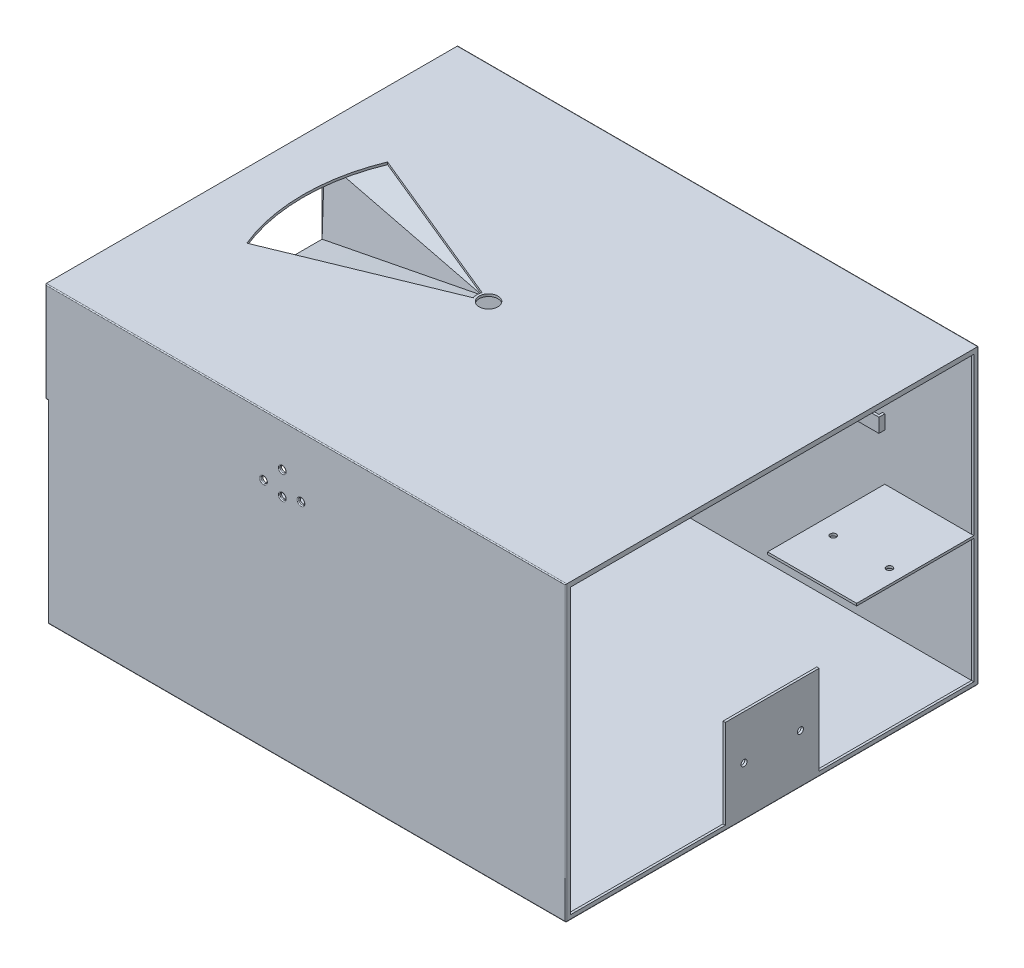
SolidWorks part; units mm, degrees
ref_plane "Front Plane" through (0, 0, 0) normal (0, 0, 1) x (1, 0, 0)
ref_plane "Top Plane" through (0, 0, 0) normal (0, 1, 0) x (1, 0, 0)
ref_plane "Right Plane" through (0, 0, 0) normal (1, 0, 0) x (0, 0, -1)
sketch "Sketch3" plane through (0, 0, 0) normal (1, 0, 0) x (0, 0, -1)
  line L0 (-124, -34.7838) -> (50, -34.7838)
  line L1 (-125, -158.7838) -> (51, -158.7838)
  line L2 (-125, -158.7838) -> (-125, -33.7838)
  line L3 (-125, -33.7838) -> (51, -33.7838)
  line L4 (51, -158.7838) -> (51, -33.7838)
  line L7 (-124, -157.7838) -> (-124, -34.7838)
  line L8 (-124, -157.7838) -> (50, -157.7838)
  line L9 (50, -157.7838) -> (50, -34.7838)
  line L11 (50, -158.7838) -> (50, -33.7838) construction
  line L13 (-125, -34.7838) -> (51, -34.7838) construction
  line L14 (-124, -158.7838) -> (-124, -33.7838) construction
  line L15 (-125, -157.7838) -> (51, -157.7838) construction
  point P8 (-123, -158.7838)
  point P9 (-123, -33.7838)
  dimension "D1" = 125
  dimension "D2" = 176
extrude "Boss-Extrude1" add sketch "Sketch3" against normal blind 220
sketch "Sketch6" plane through (-220, 0, 0) normal (-1, 0, 0) x (0, 0, 1)
  line L0 (-50, -157.7838) -> (-50, -34.7838) construction
  line L1 (-50, -82.7838) -> (-48.5, -82.7838)
  line L2 (-50, -82.7838) -> (-50, -83.7838)
  line L3 (-50, -83.7838) -> (-47.5, -83.7838)
  line L4 (-47.5, -82.7838) -> (-47.5, -83.7838)
  line L5 (124, -157.7838) -> (-50, -157.7838) construction
  line L6 (37, -34.7838) -> (37, -172.6474) construction
  line L8 (-47.5, -82.7838) -> (-47.5, -77.7838)
  line L9 (-47.5, -77.7838) -> (-48.5, -77.7838)
  line L10 (-48.5, -82.7838) -> (-48.5, -77.7838)
  line L11 (-50, -34.7838) -> (124, -34.7838) construction
  line L12 (124, -82.7838) -> (124, -83.7838)
  line L13 (121.5, -82.7838) -> (121.5, -83.7838)
  line L14 (124, -83.7838) -> (121.5, -83.7838)
  line L15 (121.5, -77.7838) -> (122.5, -77.7838)
  line L16 (121.5, -82.7838) -> (121.5, -77.7838)
  line L17 (122.5, -82.7838) -> (122.5, -77.7838)
  line L18 (124, -82.7838) -> (122.5, -82.7838)
  point P8 (-47.5, -83.2838)
  dimension "D1" = 75
  dimension "D2" = 1
  dimension "D3" = 2.5
  dimension "D4" = 1
  dimension "D5" = 5
extrude "Boss-Extrude3" add sketch "Sketch6" against normal blind 181
sketch "Sketch9" plane through (-39, 0, 0) normal (1, 0, 0) x (0, 0, -1)
  line L0 (-37, -33.7838) -> (-37, -178.9318) construction
  line L1 (-124, -83.7838) -> (-121.5, -83.7838)
  line L2 (-124, -83.7838) -> (-124, -77.7838)
  line L3 (-124, -77.7838) -> (-121.5, -77.7838)
  line L4 (-121.5, -83.7838) -> (-121.5, -77.7838)
  line L5 (51, -33.7838) -> (-125, -33.7838) construction
  line L6 (50, -83.7838) -> (47.5, -83.7838)
  line L7 (47.5, -83.7838) -> (47.5, -77.7838)
  line L8 (50, -83.7838) -> (50, -77.7838)
  line L9 (50, -77.7838) -> (47.5, -77.7838)
extrude "Boss-Extrude4" add sketch "Sketch9" along normal blind 1
sketch "Sketch11" plane through (0, -33.7838, 0) normal (0, 1, 0) x (1, 0, 0)
  line L0 (-220, -37) -> (21.9608, -37) construction
  line L1 (-220, 51) -> (-220, -125) construction
  line L2 (-193.0821, -7) -> (-124.6255, -35.1013)
  line L4 (-124.6255, -38.8987) -> (-193.0821, -67)
  arc A0 (-193.0821, -7) -> (-193.0821, -67) centre (-120, -37) ccw
  circle A1 centre (-120, -37) radius 5
  circle A2 centre (-120, -37) radius 4
  point P10 (-120, -37)
  point P14 (-120, -37)
  dimension "D1" = 158
  dimension "D3" = 8
  dimension "D4" = 10
  dimension "D2" = 100
  dimension "D5" = 30
  dimension "D6" = 30
extrude "Cut-Extrude1" cut sketch "Sketch11" against normal blind 1 contours A0 L0 A1 L2 | L0 A0 L4 A1 | A2 L0 | L0 A2
sketch "Sketch12" plane through (-220, 0, 0) normal (-1, 0, 0) x (0, 0, 1)
  line L0 (122.5, -77.7838) -> (121.5, -77.7838) construction
  line L1 (-51, -33.7838) -> (125, -33.7838)
  line L2 (-51, -33.7838) -> (-51, -76.2838)
  line L3 (-51, -76.2838) -> (125, -76.2838)
  line L4 (125, -33.7838) -> (125, -76.2838)
  line L5 (124, -34.7838) -> (124, -82.7838) construction
  point P7 (122, -77.7838)
  dimension "D1" = 1.5
  dimension "D2" = 1
extrude "Boss-Extrude5" add sketch "Sketch12" along normal blind 1
sketch "Sketch13" plane through (-221, 0, 0) normal (-1, 0, 0) x (0, 0, 1)
  line L0 (-51, -76.2838) -> (125, -76.2838) construction
  line L1 (7, -76.2838) -> (67, -76.2838)
  line L2 (7, -76.2838) -> (7, -46.2838)
  line L3 (7, -46.2838) -> (67, -46.2838)
  line L4 (67, -76.2838) -> (67, -46.2838)
  line L5 (-51, -33.7838) -> (-51, -76.2838) construction
  dimension "D1" = 60
  dimension "D2" = 58
  dimension "D3" = 30
extrude "Cut-Extrude2" cut sketch "Sketch13" against normal blind 1
sketch3d "3DSketch3"
  line L0 (-124.6255, -34.7838, 35.1013) -> (-221, -76.2838, 7)
  line L1 (-221, -76.2838, 7) -> (-221, -76.2838, 67)
  line L2 (-221, -76.2838, 67) -> (-124.6255, -34.7838, 38.8987)
surface "Surface-Fill1"
sketch3d "3DSketch4"
  line L0 (-220, -46.2838, 7) -> (-193.0821, -34.7838, 7)
  line L1 (-220, -46.2838, 67) -> (-193.0821, -34.7838, 67)
sketch3d "3DSketch5"
  line L0 (-221, -76.2838, 67) -> (-220, -46.2838, 67)
  line L1 (-220, -46.2838, 7) -> (-221, -76.2838, 7)
sketch3d "3DSketch6"
  line L0 (-193.0821, -34.7838, 7) -> (-124.6255, -33.7838, 35.1013)
sketch3d "3DSketch7"
  line L0 (-124.6255, -34.7838, 35.1013) -> (-193.0941, -34.7889, 7)
  line L1 (-220, -46.2838, 7) -> (-193.0821, -34.7838, 7) construction
  line L2 (-193.0941, -34.7889, 7) -> (-220, -46.2838, 7)
  line L3 (-220, -46.2838, 7) -> (-221, -76.2838, 7)
  line L4 (-221, -76.2838, 7) -> (-124.6255, -34.7838, 35.1013)
sketch3d "3DSketch8"
  line L0 (-220, -46.2838, 67) -> (-220, -46.2838, 7)
sketch3d "3DSketch10"
  line L0 (-124.6255, -34.7838, 35.1013) -> (-221, -76.2838, 7)
  line L1 (-221, -76.2838, 7) -> (-220, -46.2838, 7)
  line L2 (-220, -46.2838, 7) -> (-124.6255, -34.7838, 35.1013)
other "Boundary-Surface1"
sketch3d "3DSketch11"
  line L0 (-124.6255, -34.7838, 38.8987) -> (-220, -46.2838, 67)
other "Boundary-Surface2"
sketch3d "3DSketch12"
  line L0 (-220, -46.2838, 67) -> (-193.0821, -34.7838, 67)
  line L1 (-193.0821, -34.7838, 67) -> (-124.6255, -34.7838, 38.8987)
  line L2 (-124.6255, -34.7838, 38.8987) -> (-220, -46.2838, 67)
surface "Surface-Fill7" sketch "3DSketch12"
sketch3d "3DSketch13"
  line L0 (-193.0821, -34.7838, 7) -> (-124.6255, -34.7838, 35.1013)
  line L1 (-124.6255, -34.7838, 35.1013) -> (-221, -76.2838, 7)
sketch3d "3DSketch14"
  line L0 (-124.6255, -34.7838, 35.1013) -> (-221, -76.2838, 7)
  line L1 (-221, -76.2838, 7) -> (-220, -46.2838, 7)
  line L2 (-220, -46.2838, 7) -> (-124.6255, -34.7838, 35.1013)
surface "Surface-Fill8" sketch "3DSketch14"
ref_plane "Plane1" through (0, 0, 37) normal (0, 0, -1) x (-1, 0, 0)
sketch "Sketch16" plane through (0, -33.7838, 0) normal (0, 1, 0) x (1, 0, 0)
  line L0 (-120, -37) -> (-120, -162.753) construction
sketch "Sketch18" plane through (0, 0, 125) normal (0, 0, 1) x (1, 0, 0)
  line L0 (-221, -33.7838) -> (0, -33.7838) construction
  line L1 (-221, -76.2838) -> (-221, -33.7838) construction
  circle A0 centre (-120, -51.9238) radius 1.3
  circle A1 centre (-120, -61.9238) radius 1.3
  dimension "D1" = 18.14
  dimension "D2" = 101
  dimension "D3" = 2.6
  dimension "D4" = 2.6
  dimension "D5" = 10
extrude "Cut-Extrude3" cut sketch "Sketch18" against normal through all both and the other way through all
sketch "Sketch20" plane through (0, 0, 125) normal (0, 0, 1) x (1, 0, 0)
  line L0 (-221, -33.7838) -> (0, -33.7838) construction
  line L1 (-221, -76.2838) -> (-221, -33.7838) construction
  line L2 (-120, -51.9238) -> (-120, -66.5311) construction
  circle A0 centre (-128, -59.7838) radius 1.3
  circle A1 centre (-112, -59.7838) radius 1.3
  dimension "D1" = 2.6
  dimension "D2" = 26
  dimension "D3" = 93
extrude "Cut-Extrude4" cut sketch "Sketch20" against normal through all both and the other way through all
sketch "Sketch22" plane through (0, 0, 0) normal (1, 0, 0) x (0, 0, -1)
  line L0 (51, -158.7838) -> (51, -33.7838) construction
  line L1 (-125, -158.7838) -> (51, -158.7838)
  line L2 (-125, -158.7838) -> (-125, -33.7838)
  line L3 (-125, -33.7838) -> (51, -33.7838)
  line L4 (51, -158.7838) -> (51, -33.7838)
extrude "Boss-Extrude6" add sketch "Sketch22" along normal blind 1
sketch "Sketch23" plane through (1, 0, 0) normal (1, 0, 0) x (0, 0, -1)
  line L0 (-37, -162.7521) -> (-37, -23.6934) construction
  line L1 (-37, -68.75) -> (-37, 68.75) construction
  circle A0 centre (-49, -137.7838) radius 1.3
  circle A1 centre (-25, -137.7838) radius 1.3
  dimension "D2" = 2.6
extrude "Cut-Extrude5" cut sketch "Sketch23" against normal blind 2
sketch "Sketch24" plane through (1, 0, 0) normal (1, 0, 0) x (0, 0, -1)
  line L0 (-125, -158.7838) -> (51, -158.7838) construction
  line L1 (-57, -118.7838) -> (-17, -118.7838)
  line L2 (-57, -118.7838) -> (-57, -158.7838)
  line L3 (-57, -158.7838) -> (-17, -158.7838)
  line L4 (-17, -118.7838) -> (-17, -158.7838)
  line L5 (-37, -68.75) -> (-37, 68.75) construction
  line L6 (-37, -33.7838) -> (-162.753, -33.7838) construction
  line L7 (-123, -156.7838) -> (49, -156.7838)
  line L8 (-123, -156.7838) -> (-123, -35.7838)
  line L9 (-123, -35.7838) -> (49, -35.7838)
  line L10 (49, -156.7838) -> (49, -35.7838)
  line L11 (-125, -33.7838) -> (-125, -158.7838) construction
  line L12 (51, -158.7838) -> (51, -33.7838) construction
  dimension "D1" = 20
  dimension "D2" = 20
  dimension "D3" = 40
  dimension "D4" = 2
  dimension "D5" = 2
  dimension "D6" = 2
  dimension "D7" = 2
extrude "Cut-Extrude6" cut sketch "Sketch24" against normal blind 2 contours L7 L10 L9 L8 L2 L1 L4
fillet "Fillet5" radius 0.4 23 edges at (-220, -158.7838, 37) (1, -158.7838, 37) (-220, -117.5338, 125) (-220.5, -76.2838, 125) (-221, -55.0338, 125) (-110, -33.7838, 125) (1, -96.2838, 125) (-109.5, -158.7838, 125) (-120, -53.2238, 125) (-120, -63.2238, 125) (-128, -61.0838, 125) (-112, -61.0838, 125) (-221, -55.0338, -51) (-220.5, -76.2838, -51) (-220, -117.5338, -51) (-109.5, -158.7838, -51) (1, -96.2838, -51) (-110, -33.7838, -51) (-118.7, -51.9238, -51) (-118.7, -61.9238, -51) (-126.7, -59.7838, -51) (-113.3, -59.7838, -51) (-220, -157.7838, 37)
sketch "Sketch25" plane through (1, 0, 0) normal (1, 0, 0) x (0, 0, -1)
  line L0 (49, -101.7838) -> (-1, -101.7838)
  line L1 (49, -156.7838) -> (49, -35.7838) construction
  line L2 (-1, -101.7838) -> (-1, -102.7838)
  line L3 (-1, -102.7838) -> (49, -102.7838)
  line L4 (49, -102.7838) -> (49, -101.7838)
  line L5 (-17, -156.7838) -> (49, -156.7838) construction
  dimension "D1" = 55
  dimension "D2" = 1
  dimension "D3" = 50
extrude "Boss-Extrude7" add sketch "Sketch25" against normal blind 50
sketch "Sketch28" plane through (0, -101.7838, 0) normal (0, 1, 0) x (1, 0, 0)
  line L0 (-49, -1) -> (1, -1) construction
  line L1 (-49, 49) -> (-49, -1) construction
  circle A0 centre (-41, 19) radius 1.3
  circle A1 centre (-17, 19) radius 1.3
  dimension "D1" = 2.6
  dimension "D4" = 24
  dimension "D2" = 20
  dimension "D3" = 8
extrude "Cut-Extrude7" cut sketch "Sketch28" against normal blind 1
sketch "Sketch29" plane through (1, 0, 0) normal (1, 0, 0) x (0, 0, -1)
  line L0 (-1, -102.7838) -> (49, -102.7838) construction
  line L1 (-1, -101.7838) -> (49, -101.7838)
  line L2 (-1, -101.7838) -> (-1, -102.7838)
  line L3 (-1, -102.7838) -> (49, -102.7838)
  line L4 (49, -101.7838) -> (49, -102.7838)
extrude "Boss-Extrude9" add sketch "Sketch29" against normal blind 40
sketch "Sketch30" plane through (-49, 0, 0) normal (-1, 0, 0) x (0, 0, 1)
  line L1 (-49, -101.7838) -> (1, -101.7838)
  line L2 (-49, -101.7838) -> (-49, -102.7838)
  line L3 (-49, -102.7838) -> (1, -102.7838)
  line L4 (1, -101.7838) -> (1, -102.7838)
extrude "Cut-Extrude9" cut sketch "Sketch30" against normal blind 12
sketch "Sketch31" plane through (0, -101.7838, 0) normal (0, 1, 0) x (1, 0, 0)
  line L0 (-37, -1) -> (-37, 49) construction
  line L1 (-37, -1) -> (1, -1) construction
  circle A0 centre (-29, 19) radius 1.3
  circle A1 centre (-5, 19) radius 1.3
  dimension "D1" = 8
  dimension "D2" = 20
  dimension "D3" = 24
extrude "Cut-Extrude11" cut sketch "Sketch31" against normal up to next
sketch "Sketch32" plane through (1, 0, 0) normal (1, 0, 0) x (0, 0, -1)
  line L0 (49, -156.7838) -> (49, -102.7838) construction
  line L1 (-1, -102.7838) -> (49, -102.7838)
  line L2 (-1, -102.7838) -> (-1, -103.7838)
  line L3 (-1, -103.7838) -> (49, -103.7838)
  line L4 (49, -102.7838) -> (49, -103.7838)
  dimension "D1" = 1
extrude "Boss-Extrude10" add sketch "Sketch32" against normal blind 38
sketch "Sketch33" plane through (0, -101.7838, 0) normal (0, 1, 0) x (1, 0, 0)
  circle A0 centre (-29, 19) radius 1.3
  circle A1 centre (-5, 19) radius 1.3
extrude "Cut-Extrude12" cut sketch "Sketch33" against normal blind 38
sketch "Sketch34" plane through (1, 0, 0) normal (1, 0, 0) x (0, 0, -1)
  line L1 (-1, -101.7838) -> (49, -101.7838)
  line L2 (-1, -101.7838) -> (-1, -102.7838)
  line L3 (-1, -102.7838) -> (49, -102.7838)
  line L4 (49, -101.7838) -> (49, -102.7838)
  dimension "D1" = 1
extrude "Cut-Extrude13" cut sketch "Sketch34" against normal blind 38
